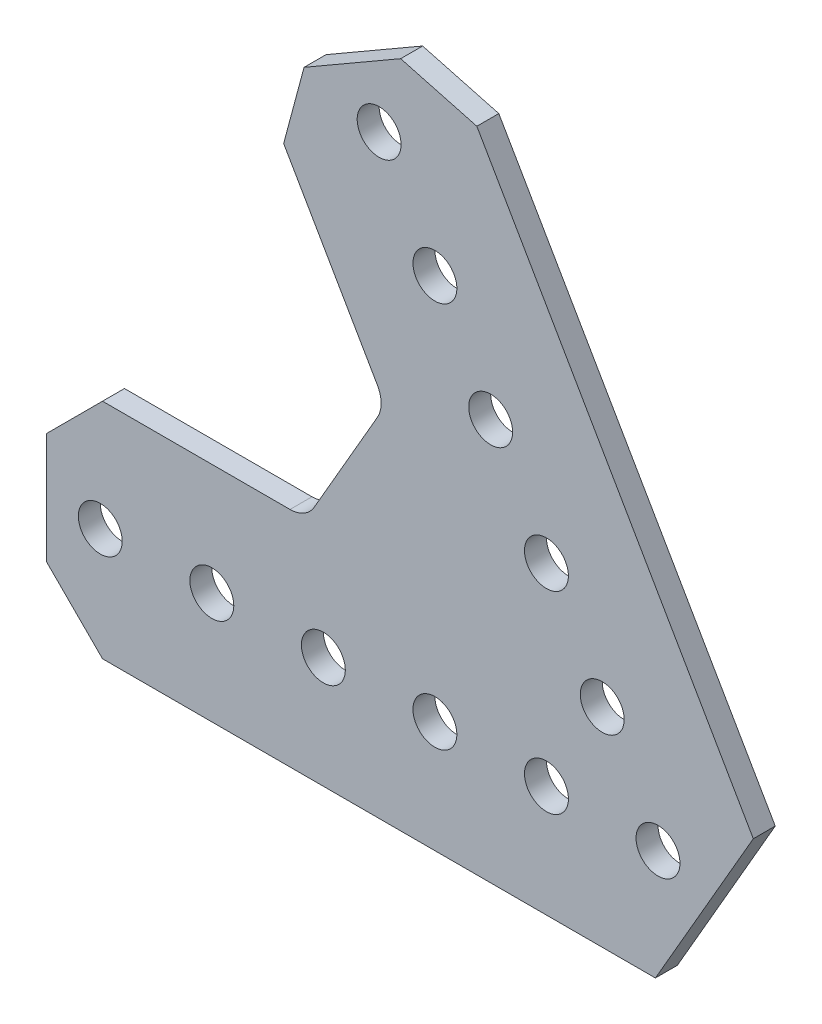
SolidWorks part; units mm, degrees
material "5052-H32"
ref_plane "Front Plane" through (0, 0, 0) normal (0, 0, 1) x (1, 0, 0)
ref_plane "Top Plane" through (0, 0, 0) normal (0, 1, 0) x (1, 0, 0)
ref_plane "Right Plane" through (0, 0, 0) normal (1, 0, 0) x (0, 0, -1)
ref_plane "Plane1" through (0, 0, -1.25) normal (0, 0, -1) x (-1, 0, 0)
sketch "Sketch1" plane through (0, 0, -1.25) normal (0, 0, -1) x (-1, 0, 0)
  line L0 (0.2933, -12.7) -> (63.246, -12.7)
  line L1 (63.246, -12.7) -> (69.596, -6.35)
  line L2 (69.596, -6.35) -> (69.596, 6.35)
  line L3 (69.596, 6.35) -> (63.246, 12.7)
  line L4 (63.246, 12.7) -> (41.8978, 12.7)
  line L5 (39.1482, 14.2875) -> (31.9474, 26.7595)
  line L6 (31.9474, 29.9345) -> (42.6215, 48.4226)
  line L7 (42.6215, 48.4226) -> (40.2973, 57.0969)
  line L8 (40.2973, 57.0969) -> (29.2987, 63.4469)
  line L9 (29.2987, 63.4469) -> (20.6245, 61.1226)
  line L10 (20.6245, 61.1226) -> (-10.8519, 6.604)
  line L11 (-10.8519, 6.604) -> (0.2933, -12.7)
  circle A0 centre (12.7, 0) radius 2.5
  circle A1 centre (25.4, 0) radius 2.5
  circle A2 centre (38.1, 0) radius 2.5
  circle A3 centre (0, 0) radius 2.5
  circle A4 centre (63.5, 0) radius 2.5
  circle A5 centre (50.8, 0) radius 2.5
  circle A6 centre (31.75, 54.9926) radius 2.5
  circle A7 centre (25.4, 43.9941) radius 2.5
  circle A8 centre (19.05, 32.9956) radius 2.5
  circle A9 centre (12.7, 21.997) radius 2.5
  circle A10 centre (6.35, 10.9985) radius 2.5
  arc A11 (41.8978, 12.7) -> (39.1482, 14.2875) centre (41.8978, 15.875) cw
  arc A12 (31.9474, 26.7595) -> (31.9474, 29.9345) centre (34.697, 28.347) cw
extrude "Boss-Extrude1" add sketch "Sketch1" against normal blind 2.5
